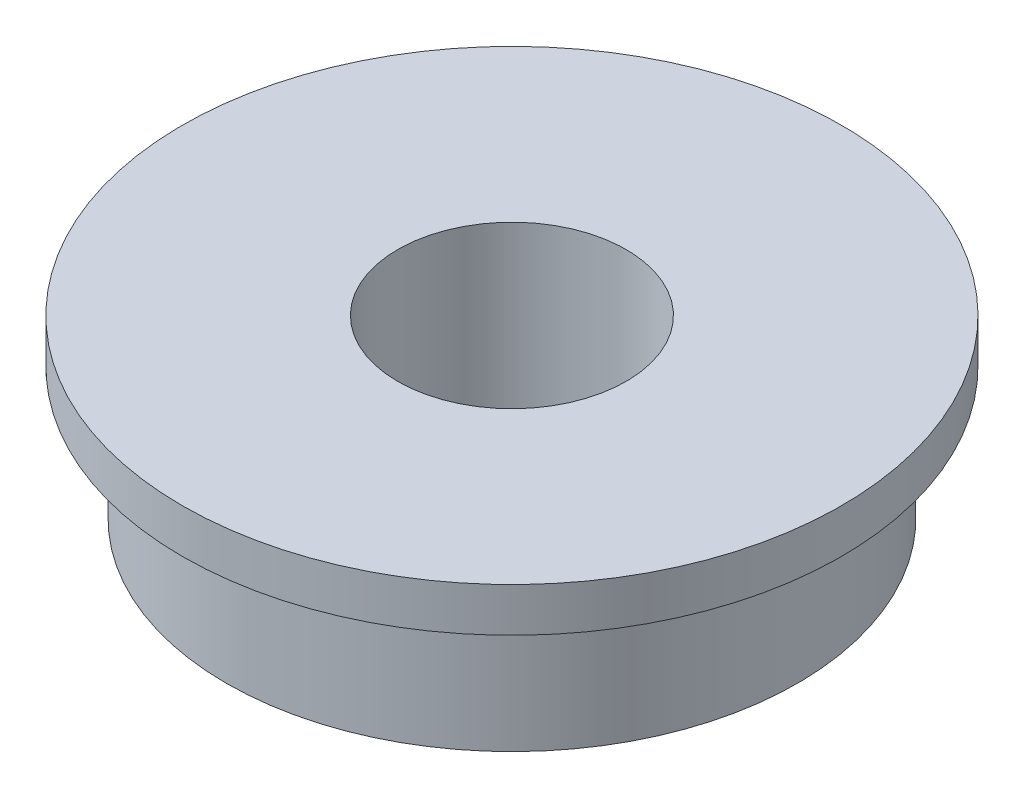
SolidWorks part; units mm, degrees
material "A286 铁基超合金"
ref_plane "前视基准面" through (0, 0, 0) normal (0, 0, 1) x (1, 0, 0)
ref_plane "上视基准面" through (0, 0, 0) normal (0, 1, 0) x (1, 0, 0)
ref_plane "右视基准面" through (0, 0, 0) normal (1, 0, 0) x (0, 0, -1)
sketch "草图1" plane through (0, 0, 0) normal (0, 1, 0) x (1, 0, 0)
  circle A0 centre (0, 0) radius 2.6
  circle A1 centre (0, 0) radius 6.5
  dimension "D1" = 5.2
  dimension "D2" = 13
extrude "凸台-拉伸1" add sketch "草图1" along normal blind 4
sketch "草图2" plane through (0, 4, 0) normal (0, 1, 0) x (1, 0, 0)
  circle A0 centre (0, 0) radius 2.6
  circle A1 centre (0, 0) radius 7.5
  circle A2 centre (0, 0) radius 2.6 construction
  dimension "D1" = 15
extrude "凸台-拉伸2" add sketch "草图2" against normal blind 1
